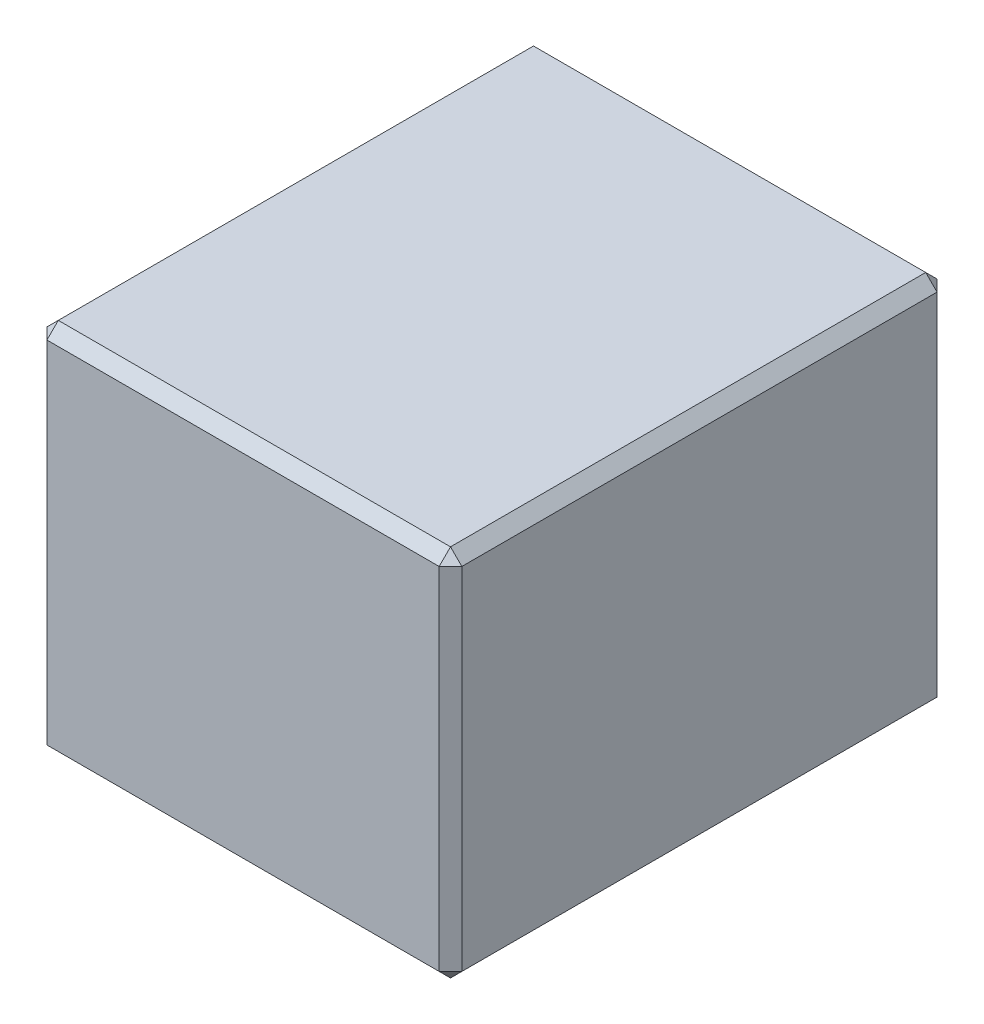
SolidWorks part; units mm, degrees
ref_plane "Front Plane" through (0, 0, 0) normal (0, 0, 1) x (1, 0, 0)
ref_plane "Top Plane" through (0, 0, 0) normal (0, 1, 0) x (1, 0, 0)
ref_plane "Right Plane" through (0, 0, 0) normal (1, 0, 0) x (0, 0, -1)
sketch "Sketch2" plane through (0, 0, 0) normal (0, 1, 0) x (1, 0, 0)
  line L1 (-508, -609.6) -> (508, -609.6)
  line L2 (-508, -609.6) -> (-508, 609.6)
  line L3 (-508, 609.6) -> (508, 609.6)
  line L4 (508, -609.6) -> (508, 609.6)
  line L5 (-508, -609.6) -> (508, 609.6) construction
  line L6 (-508, 609.6) -> (508, -609.6) construction
  point P0 (0, 0)
  dimension "D1" = 1219.2
  dimension "D2" = 1016
extrude "Boss-Extrude1" add sketch "Sketch2" along normal blind 914.4
chamfer "Chamfer1" distance 27.78 angle 45 12 edges at (0, 0, 609.6) (-508, 457.2, 609.6) (-508, 0, 0) (-508, 457.2, -609.6) (0, 0, -609.6) (0, 914.4, 609.6) (-508, 914.4, 0) (0, 914.4, -609.6) (508, 457.2, 609.6) (508, 914.4, 0) (508, 457.2, -609.6) (508, 0, 0)
